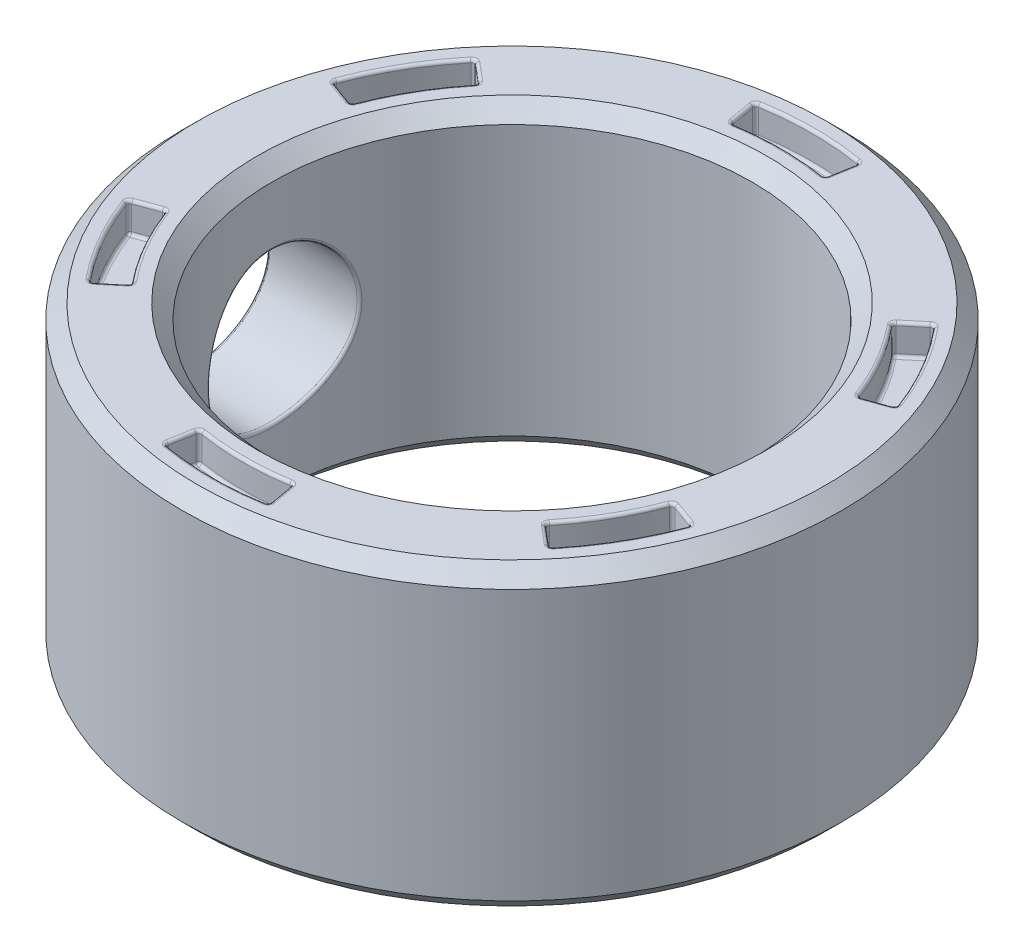
SolidWorks part; units mm, degrees
ref_plane "Front Plane" through (0, 0, 0) normal (0, 0, 1) x (1, 0, 0)
ref_plane "Top Plane" through (0, 0, 0) normal (0, 1, 0) x (1, 0, 0)
ref_plane "Right Plane" through (0, 0, 0) normal (1, 0, 0) x (0, 0, -1)
sketch "Sketch1" plane through (0, 0, 0) normal (0, 1, 0) x (1, 0, 0)
  circle A0 centre (0, 0) radius 11
  circle A1 centre (0, 0) radius 8
  dimension "D1" = 22
  dimension "D2" = 16
extrude "Boss-Extrude1" add sketch "Sketch1" along normal blind 10
chamfer "Chamfer1" distance 0.5 angle 45 4 edges at (0, 0, 8) (0, 0, 11) (0, 10, 11) (0, 10, 8)
sketch "Sketch2" plane through (0, 10, 0) normal (0, 1, 0) x (1, 0, 0)
  line L0 (0, 0) -> (0, 10) construction
  line L1 (0, 0) -> (1.7365, 9.8481) construction
  line L2 (0, 0) -> (-1.7365, 9.8481) construction
  line L3 (-1.7365, 9.8481) -> (-1.5628, 8.8633)
  line L4 (1.7365, 9.8481) -> (1.5628, 8.8633)
  circle A0 centre (0, 0) radius 10 construction
  circle A1 centre (0, 0) radius 9 construction
  arc A2 (1.7365, 9.8481) -> (-1.7365, 9.8481) centre (0, 0) ccw
  arc A3 (1.5628, 8.8633) -> (-1.5628, 8.8633) centre (0, 0) ccw
  dimension "D1" = 20
  dimension "D2" = 18
  dimension "D3" = 10
extrude "Cut-Extrude1" cut sketch "Sketch2" against normal blind 1
fillet "Fillet1" radius 0.1 12 edges at (1.7365, 9.5, -9.8481) (1.5628, 9.5, -8.8633) (1.6497, 10, -9.3557) (1.6497, 9, -9.3557) (-1.5628, 9.5, -8.8633) (-1.7365, 9.5, -9.8481) (-1.6497, 10, -9.3557) (-1.6497, 9, -9.3557) (0, 10, -10) (0, 9, -10) (0, 10, -9) (0, 9, -9)
pattern_circular "CirPattern1" count 6 over 360 about axis through (0, 0, 0) along (0, 1, 0) of "Cut-Extrude1", "Fillet1"
sketch "Sketch3" plane through (0, 0, 0) normal (1, 0, 0) x (0, 0, -1)
  line L1 (0, 10) -> (0, 0) construction
  line L2 (8.5, 10) -> (-8.5, 10) construction
  circle A0 centre (0, 5) radius 2.5
  dimension "D1" = 5
extrude "Cut-Extrude2" cut sketch "Sketch3" against normal up to next
fillet "Fillet2" radius 0.1 2 edges at (-7.6123, 5.4442, 2.4602) (-10.724, 5.504, 2.4487)
